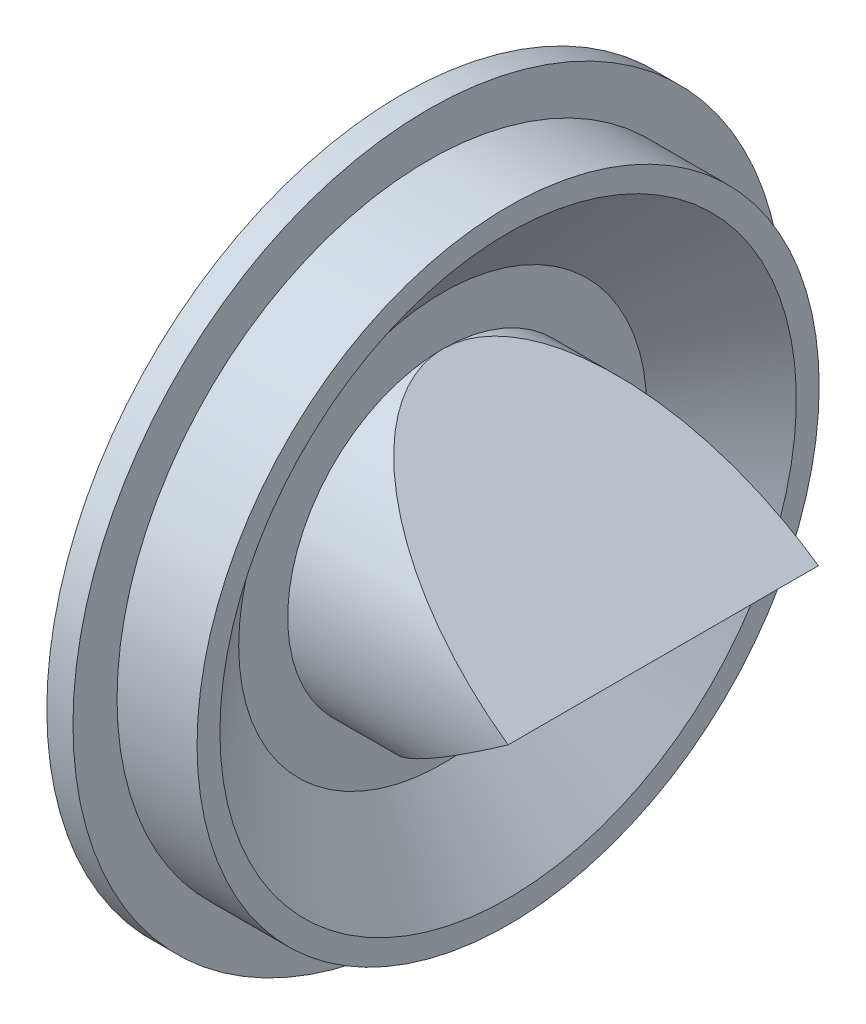
SolidWorks part; units mm, degrees
ref_plane "Front" through (0, 0, 0) normal (0, 0, 1) x (1, 0, 0)
ref_plane "Top" through (0, 0, 0) normal (0, 1, 0) x (1, 0, 0)
ref_plane "Right" through (0, 0, 0) normal (1, 0, 0) x (0, 0, -1)
sketch "Sketch3" plane through (0, 0, 0) normal (-1, 0, 0) x (0, 0, 1)
  circle A0 centre (0, 0) radius 9.5
extrude "Boss-Extrude1" add sketch "Sketch3" against normal blind 16
sketch "Sketch4" plane through (0, 0, 0) normal (0, 0, 1) x (1, 0, 0)
  line L0 (0, 0) -> (24.256, 0) construction
  line L2 (16, -9.5) -> (16, 9.5) construction
  line L7 (2.5, 9.5) -> (18.0589, 17.2679)
  line L8 (2.5, 9.5) -> (16, 0)
  line L11 (2.5, -9.5) -> (16, 0)
  line L12 (2.5, -9.5) -> (18.0589, -17.2679)
  line L13 (18.0589, -17.2679) -> (18.0589, 17.2679)
  point P11 (18.0589, 0)
extrude "Cut-Extrude1" cut sketch "Sketch4" against normal through all both and the other way through all
shell "Shell7" thickness 0.3
sketch "Sketch1" plane through (0, 0, 0) normal (0, 0, 1) x (1, 0, 0)
  line L0 (0, 18.75) -> (0, 21.75)
  line L1 (0, 21.75) -> (1.6, 21.75)
  line L2 (1.6, 21.75) -> (1.6, 19.05)
  line L3 (1.6, 19.05) -> (6.5, 19.05)
  line L4 (6.5, 19.05) -> (6.5, 17.65)
  line L5 (0, 18.75) -> (6.2, 18.75)
  line L6 (0, 0) -> (26.4761, 0) construction
  line L7 (6.5, 17.65) -> (2.5, 12.5)
  line L8 (2.5, 12.5) -> (2.5, 9.5)
  line L9 (6.2, 18.75) -> (6.2, 17.7528)
  line L10 (6.2, 17.7528) -> (2.2, 12.6028)
  line L11 (6.2, 19.05) -> (6.2, 17.7528) construction
  line L12 (2.2, 12.6028) -> (2.2, 9.5)
  line L13 (6.2, 17.7528) -> (2.2631, 12.684) construction
  line L14 (2.2, 12.5) -> (2.2, 9.5) construction
  line L15 (2.2, 9.5) -> (2.5, 9.5)
  dimension "D1" = 37.5
  dimension "D2" = 43.5
  dimension "D3" = 1.6
  dimension "D4" = 0.3
  dimension "D6" = 0.3
  dimension "D7" = 6.5
  dimension "D8" = 4
  dimension "D9" = 25
  dimension "D10" = 19
  dimension "D11" = 0.3
revolve "Revolve1" add sketch "Sketch1" angle 360 about L6
sketch "Sketch8" plane through (2.2, 0, 0) normal (-1, 0, 0) x (0, 0, 1)
  circle A0 centre (0, 0) radius 10.7058
extrude "Cut-Extrude5" cut sketch "Sketch8" along normal blind 10
